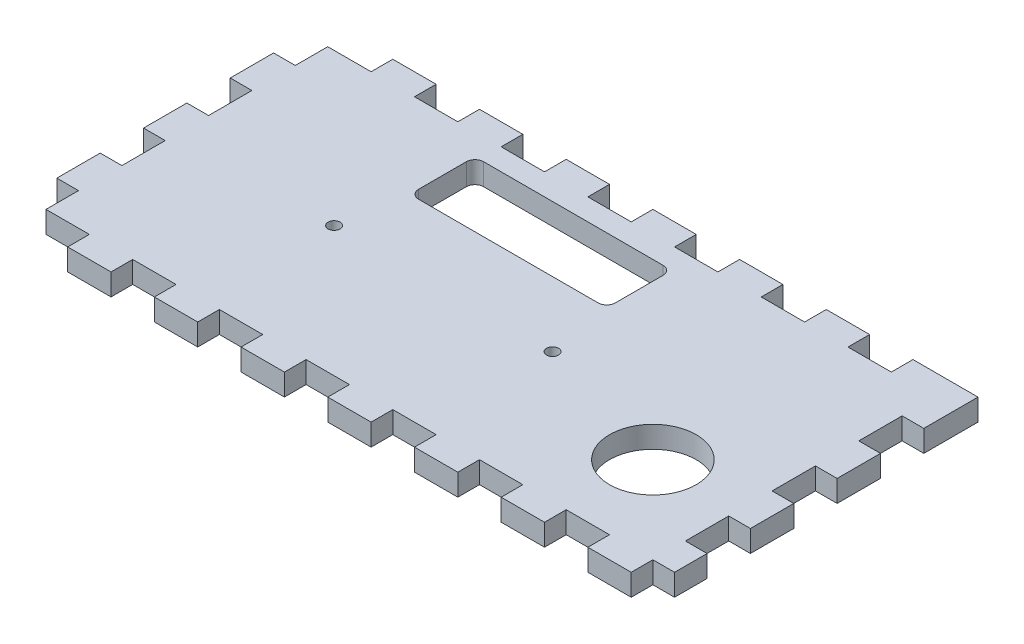
SolidWorks part; units mm, degrees
material "Pine"
ref_plane "Front Plane" through (0, 0, 0) normal (0, 0, 1) x (1, 0, 0)
ref_plane "Top Plane" through (0, 0, 0) normal (0, 1, 0) x (1, 0, 0)
ref_plane "Right Plane" through (0, 0, 0) normal (1, 0, 0) x (0, 0, -1)
sketch "Sketch1" plane through (0, 0, 0) normal (0, 1, 0) x (1, 0, 0)
  line L1 (0, 0) -> (431.8, 0)
  line L2 (0, 0) -> (0, 95.25)
  line L3 (0, 95.25) -> (431.8, 95.25)
  line L4 (431.8, 0) -> (431.8, 95.25)
  dimension "D1" = 431.8
  dimension "D2" = 95.25
extrude "Boss-Extrude1" add sketch "Sketch1" along normal blind 6.35
sketch "Sketch2" plane through (0, 6.35, 0) normal (0, 1, 0) x (1, 0, 0)
  line L1 (431.8, 95.25) -> (0, 95.25) construction
  line L2 (6.35, 95.25) -> (19.05, 95.25)
  line L3 (6.35, 95.25) -> (6.35, 88.9)
  line L4 (6.35, 88.9) -> (19.05, 88.9)
  line L7 (19.05, 95.25) -> (19.05, 88.9)
  line L8 (0, 0) -> (431.8, 0) construction
  line L9 (6.35, 0) -> (19.05, 0)
  line L10 (6.35, 0) -> (6.35, 6.35)
  line L11 (6.35, 6.35) -> (19.05, 6.35)
  line L12 (19.05, 0) -> (19.05, 6.35)
  line L13 (0, 95.25) -> (0, 0) construction
  dimension "D1" = 6.35
  dimension "D2" = 12.7
  dimension "D3" = 6.35
extrude "Cut-Extrude1" cut sketch "Sketch2" against normal through all
pattern_linear "LPattern1" count 17 spacing 25.4 along (1, 0, 0) of "Cut-Extrude1"
sketch "Sketch3" plane through (0, 6.35, 0) normal (0, 1, 0) x (1, 0, 0)
  line L1 (6.35, 88.9) -> (0, 88.9)
  line L2 (6.35, 88.9) -> (6.35, 95.25)
  line L3 (6.35, 95.25) -> (0, 95.25)
  line L4 (0, 88.9) -> (0, 95.25)
  line L5 (6.35, 6.35) -> (0, 6.35)
  line L6 (6.35, 6.35) -> (6.35, 0)
  line L7 (6.35, 0) -> (0, 0)
  line L8 (0, 6.35) -> (0, 0)
  line L9 (425.45, 88.9) -> (431.8, 88.9)
  line L10 (425.45, 88.9) -> (425.45, 95.25)
  line L11 (425.45, 95.25) -> (431.8, 95.25)
  line L12 (431.8, 88.9) -> (431.8, 95.25)
  line L13 (425.45, 6.35) -> (431.8, 6.35)
  line L14 (425.45, 6.35) -> (425.45, 0)
  line L15 (425.45, 0) -> (431.8, 0)
  line L16 (431.8, 6.35) -> (431.8, 0)
extrude "Cut-Extrude2" cut sketch "Sketch3" against normal through all
sketch "Sketch5" plane through (0, 6.35, 0) normal (0, 1, 0) x (1, 0, 0)
  line L0 (311.15, 88.9) -> (311.15, 6.35) construction
  line L1 (190.5, 88.9) -> (190.5, 6.35) construction
  line L2 (184.15, 88.9) -> (196.85, 88.9) construction
  line L3 (196.85, 6.35) -> (184.15, 6.35) construction
  line L5 (190.5, 53.975) -> (184.15, 53.975)
  line L6 (190.5, 53.975) -> (190.5, 41.275)
  line L7 (190.5, 41.275) -> (184.15, 41.275)
  line L8 (184.15, 53.975) -> (184.15, 41.275)
  line L9 (311.15, 53.975) -> (304.8, 53.975)
  line L10 (311.15, 53.975) -> (311.15, 41.275)
  line L11 (311.15, 41.275) -> (304.8, 41.275)
  line L12 (304.8, 53.975) -> (304.8, 41.275)
  point P18 (190.5, 47.625)
  point P19 (311.15, 47.625)
  dimension "D1" = 6.35
  dimension "D2" = 12.7
extrude "Cut-Extrude4" cut sketch "Sketch5" against normal through all
pattern_linear "LPattern2" count 2 spacing 25.4 along (0, 0, -1) count 2 spacing 25.4 along (0, 0, 1) of "Cut-Extrude4"
sketch "Sketch6" plane through (0, 6.35, 0) normal (0, 1, 0) x (1, 0, 0)
  line L0 (190.5, 47.625) -> (304.8, 47.625) construction
  line L1 (190.5, 41.275) -> (190.5, 53.975) construction
  line L2 (304.8, 53.975) -> (304.8, 41.275) construction
  line L4 (304.8, 24.6063) -> (190.5, 24.6062)
  line L5 (304.8, 24.6063) -> (304.8, 70.6438)
  line L6 (304.8, 70.6438) -> (190.5, 70.6437)
  line L7 (190.5, 24.6062) -> (190.5, 70.6437)
  line L8 (304.8, 24.6063) -> (190.5, 70.6437) construction
  line L9 (304.8, 70.6438) -> (190.5, 24.6062) construction
  point P6 (247.65, 47.625)
  dimension "D1" = 46.0375
  dimension "D2" = 114.3
extrude "Cut-Extrude5" cut sketch "Sketch6" against normal through all
sketch "Sketch7" plane through (0, 6.35, 0) normal (0, 1, 0) x (1, 0, 0)
  line L0 (0, 44.45) -> (431.8, 44.45) construction
  line L1 (0, 88.9) -> (0, 6.35) construction
  line L2 (431.8, 6.35) -> (431.8, 88.9) construction
  line L3 (323.85, 0) -> (336.55, 0) construction
  circle A0 centre (52.65, 44.45) radius 1.75
  circle A1 centre (116.65, 44.45) radius 1.75
  circle A2 centre (315.15, 44.45) radius 1.75
  circle A3 centre (379.15, 44.45) radius 1.75
  dimension "D6" = 3.5
  dimension "D1" = 44.45
  dimension "D2" = 64
  dimension "D3" = 64
  dimension "D4" = 116.65
  dimension "D5" = 116.65
extrude "Cut-Extrude6" cut sketch "Sketch7" against normal through all
sketch "Sketch8" plane through (0, 6.35, 0) normal (0, 1, 0) x (1, 0, 0)
  line L0 (0, 88.9) -> (0, 6.35) construction
  line L1 (0, 88.9) -> (6.35, 88.9)
  line L2 (0, 88.9) -> (0, 79.375)
  line L3 (0, 79.375) -> (6.35, 79.375)
  line L4 (6.35, 88.9) -> (6.35, 79.375)
  line L5 (0, 6.35) -> (6.35, 6.35)
  line L6 (0, 6.35) -> (0, 15.875)
  line L7 (0, 15.875) -> (6.35, 15.875)
  line L8 (6.35, 6.35) -> (6.35, 15.875)
  line L9 (0, 28.575) -> (6.35, 28.575)
  line L10 (0, 28.575) -> (0, 41.275)
  line L11 (0, 41.275) -> (6.35, 41.275)
  line L12 (6.35, 28.575) -> (6.35, 41.275)
  line L13 (190.5, 53.975) -> (184.15, 53.975) construction
  line L14 (0, 66.675) -> (6.35, 66.675)
  line L15 (0, 66.675) -> (0, 53.975)
  line L16 (0, 53.975) -> (6.35, 53.975)
  line L17 (6.35, 66.675) -> (6.35, 53.975)
  line L18 (184.15, 41.275) -> (190.5, 41.275) construction
  line L19 (190.5, 28.575) -> (184.15, 28.575) construction
  line L20 (19.05, 0) -> (19.05, 6.35) construction
  line L21 (190.5, 79.375) -> (184.15, 79.375) construction
  line L22 (184.15, 15.875) -> (190.5, 15.875) construction
extrude "Cut-Extrude7" cut sketch "Sketch8" against normal through all
pattern_linear "LPattern3" count 2 spacing 425.45 along (1, 0, 0) of "Cut-Extrude7"
sketch "Sketch9" plane through (0, 6.35, 0) normal (0, 1, 0) x (1, 0, 0)
  line L0 (431.8, 15.875) -> (431.8, 28.575) construction
  line L1 (190.5, 95.25) -> (431.8, 95.25)
  line L2 (190.5, 95.25) -> (190.5, 0)
  line L3 (190.5, 0) -> (431.8, 0)
  line L4 (431.8, 95.25) -> (431.8, 0)
  line L5 (209.55, 95.25) -> (196.85, 95.25) construction
  line L6 (190.5, 66.675) -> (190.5, 53.975) construction
  line L7 (196.85, 0) -> (209.55, 0) construction
extrude "Cut-Extrude8" cut sketch "Sketch9" against normal through all
sketch "Sketch11" plane through (0, 6.35, 0) normal (0, 1, 0) x (1, 0, 0)
  line L1 (184.15, 95.25) -> (190.5, 95.25)
  line L2 (184.15, 95.25) -> (184.15, 88.9)
  line L3 (184.15, 88.9) -> (190.5, 88.9)
  line L4 (190.5, 95.25) -> (190.5, 88.9)
extrude "Boss-Extrude2" add sketch "Sketch11" against normal through all
sketch "Sketch12" plane through (0, 6.35, 0) normal (0, 1, 0) x (1, 0, 0)
  line L0 (57.15, 88.9) -> (69.85, 88.9) construction
  line L1 (55.825, 63.5) -> (113.475, 63.5)
  line L2 (55.825, 63.5) -> (55.825, 82.55)
  line L3 (55.825, 82.55) -> (113.475, 82.55)
  line L4 (113.475, 63.5) -> (113.475, 82.55)
  circle A0 centre (52.65, 44.45) radius 1.75 construction
  circle A1 centre (116.65, 44.45) radius 1.75 construction
  dimension "D1" = 3.175
  dimension "D2" = 6.35
  dimension "D3" = 3.175
  dimension "D4" = 19.05
extrude "Cut-Extrude10" cut sketch "Sketch12" against normal through all
fillet "Fillet1" radius 2.54 4 edges at (113.475, 3.175, -63.5) (113.475, 3.175, -82.55) (55.825, 3.175, -82.55) (55.825, 3.175, -63.5)
sketch "Sketch13" plane through (0, 6.35, 0) normal (0, 1, 0) x (1, 0, 0)
  line L0 (171.45, 6.35) -> (158.75, 6.35) construction
  line L1 (184.15, 28.575) -> (184.15, 15.875) construction
  circle A0 centre (158.75, 31.75) radius 12.7
  dimension "D2" = 25.4
  dimension "D3" = 25.4
  dimension "D1" = 25.4
extrude "Cut-Extrude11" cut sketch "Sketch13" against normal through all
